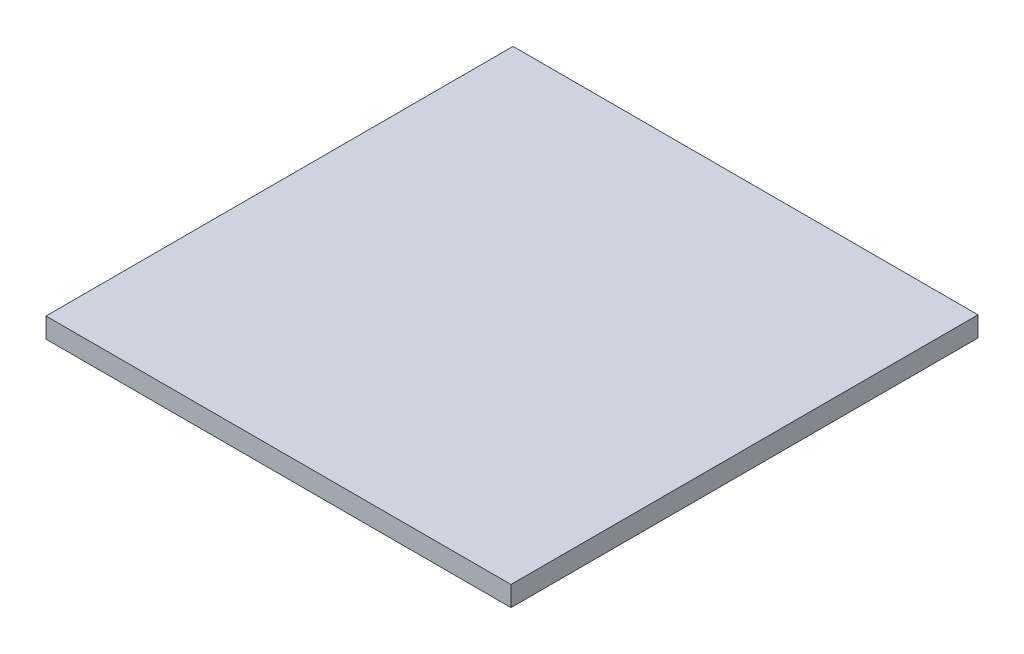
SolidWorks part; units mm, degrees
ref_plane "Front Plane" through (0, 0, 0) normal (0, 0, 1) x (1, 0, 0)
ref_plane "Top Plane" through (0, 0, 0) normal (0, 1, 0) x (1, 0, 0)
ref_plane "Right Plane" through (0, 0, 0) normal (1, 0, 0) x (0, 0, -1)
sketch "Sketch1" plane through (0, 0, 0) normal (0, 1, 0) x (1, 0, 0)
  line L1 (0, 0) -> (22, 0)
  line L2 (0, 0) -> (0, 22.098)
  line L3 (0, 22.098) -> (22, 22.098)
  line L4 (22, 0) -> (22, 22.098)
  dimension "D1" = 22
  dimension "D2" = 22.098
extrude "Boss-Extrude1" add sketch "Sketch1" along normal blind 0.95
